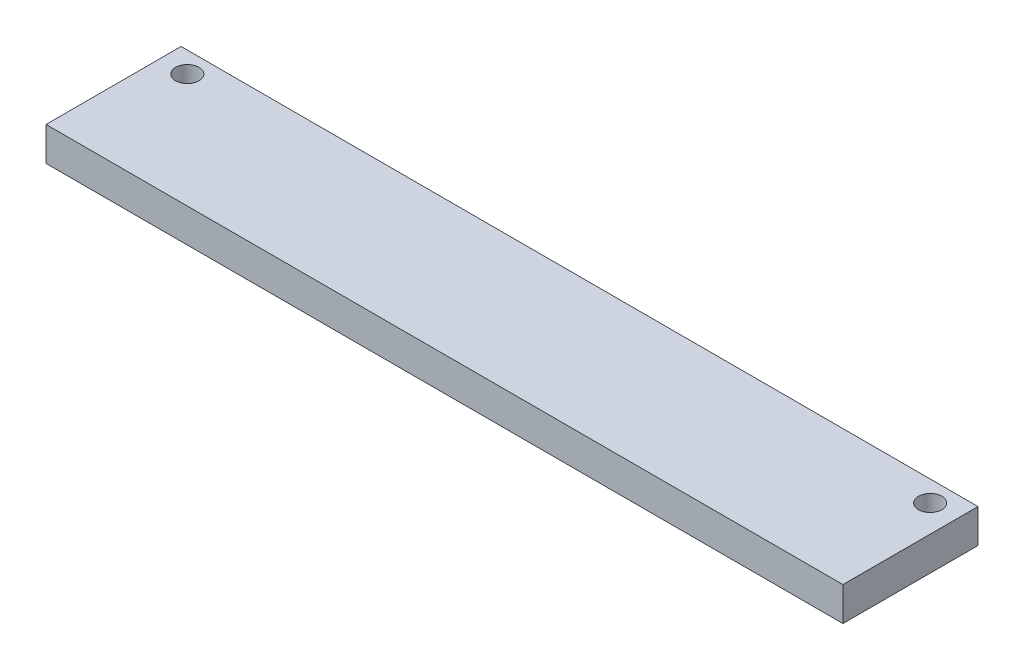
SolidWorks part; units mm, degrees
ref_plane "Plano frontal" through (0, 0, 0) normal (0, 0, 1) x (1, 0, 0)
ref_plane "Plano superior" through (0, 0, 0) normal (0, 1, 0) x (1, 0, 0)
ref_plane "Plano direito" through (0, 0, 0) normal (1, 0, 0) x (0, 0, -1)
sketch "Esboço1" plane through (0, 0, 0) normal (0, 1, 0) x (1, 0, 0)
  line L1 (-44.8956, 5.695) -> (30.0344, 5.695)
  line L2 (-44.8956, 5.695) -> (-44.8956, -7.005)
  line L3 (-44.8956, -7.005) -> (30.0344, -7.005)
  line L4 (30.0344, 5.695) -> (30.0344, -7.005)
extrude "Ressalto-extrusão1" add sketch "Esboço1" along normal blind 3.175
sketch "Esboço2" plane through (0, 0, 0) normal (0, -1, 0) x (1, 0, 0)
  line L0 (30.0344, 7.005) -> (30.0344, -5.695) construction
  line L1 (-44.8956, -5.695) -> (-44.8956, 7.005) construction
  circle A0 centre (27.4944, -3.7392) radius 1.1
  circle A1 centre (-42.3556, -3.7392) radius 1.1
  dimension "D1" = 69.85
  dimension "D2" = 2.54
  dimension "D3" = 2.54
extrude "Corte-extrusão1" cut sketch "Esboço2" against normal blind 12.175
